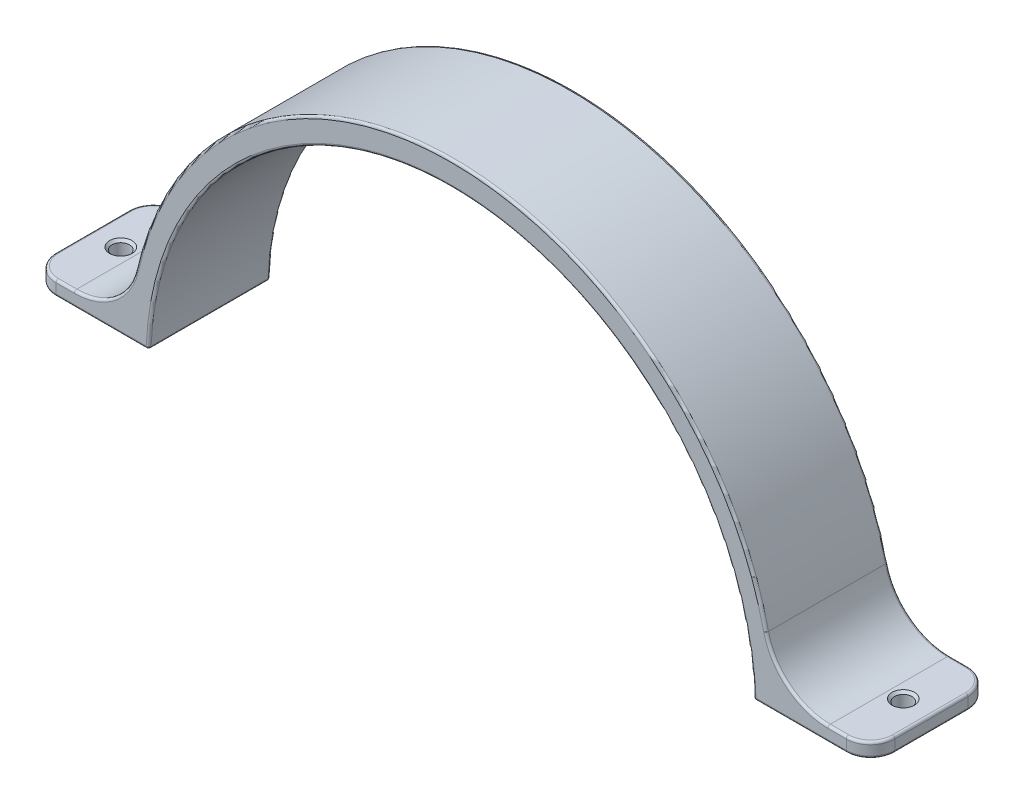
SolidWorks part; units mm, degrees
ref_plane "Plano frontal" through (0, 0, 0) normal (0, 0, 1) x (1, 0, 0)
ref_plane "Plano superior" through (0, 0, 0) normal (0, 1, 0) x (1, 0, 0)
ref_plane "Plano direito" through (0, 0, 0) normal (1, 0, 0) x (0, 0, -1)
sketch "Sketch1" plane through (0, 0, 0) normal (0, 0, 1) x (1, 0, 0)
  line L0 (0, -13.75) -> (0, 13.75) construction
  line L1 (-86.15, -27) -> (-66.15, -27)
  line L2 (-86.15, -27) -> (-86.15, -30)
  line L3 (-86.15, -30) -> (-62.15, -30)
  line L4 (86.15, -30) -> (62.15, -30)
  line L5 (86.15, -27) -> (86.15, -30)
  line L6 (86.15, -27) -> (66.15, -27)
  line L7 (-62.15, -30) -> (62.15, -30) construction
  line L8 (0, 30) -> (0, -30) construction
  arc A2 (-62.15, -30) -> (62.15, -30) centre (0, -32.1885) cw
  arc A3 (-66.15, -27) -> (66.15, -27) centre (0, -31.2889) cw
  point P4 (20.0951, 6.1437)
  point P15 (16.9603, 5.1853)
  point P16 (0, 0)
  dimension "D3" = 4
  dimension "D4" = 124.3
  dimension "D5" = 5
  dimension "D6" = 60
  dimension "D1" = 3
  dimension "D2" = 20
extrude "Boss-Extrude1" add sketch "Sketch1" along normal mid plane 25
sketch "Sketch2" plane through (0, 0, 0) normal (0, 1, 0) x (1, 0, 0)
  line L3 (0, -13.75) -> (0, 13.75) construction
  line L5 (-86.15, -12.5) -> (-86.15, 12.5) construction
  line L7 (-66.15, -12.5) -> (-66.15, 12.5) construction
  line L8 (-66.15, 12.5) -> (-86.15, 12.5) construction
  line L9 (-66.15, -12.5) -> (-86.15, -12.5) construction
  circle A0 centre (-80.35, 0) radius 1.5 construction
  circle A1 centre (-80.35, 0) radius 1.8
  circle A2 centre (80.35, 0) radius 1.5 construction
  circle A3 centre (80.35, 0) radius 1.8
  dimension "D1" = 3
  dimension "D3" = 4
  dimension "D4" = 12.4
  dimension "D5" = 12.5
  dimension "D6" = 12.5
  dimension "D7" = 160.7
  dimension "D2" = 0.3
extrude "Cut-Extrude4" cut sketch "Sketch2" against normal through all both and the other way through all
chamfer "Chamfer1" distance 0.5 angle 45 2 edges at (-80.35, -27, -1.8) (80.35, -27, -1.8)
fillet "Fillet1" radius 13 2 edges at (-66.15, -27, 0) (66.15, -27, 0)
fillet "Fillet2" radius 5 4 edges at (86.15, -28.5, 12.5) (86.15, -28.5, -12.5) (-86.15, -28.5, -12.5) (-86.15, -28.5, 12.5)
fillet "Fillet3" radius 0.5 30 edges at (-84.6855, -30, -11.0355) (-86.15, -30, 0) (-84.6855, -30, 11.0355) (84.6855, -27, 11.0355) (86.15, -27, 0) (84.6855, -27, -11.0355) (-84.6855, -27, -11.0355) (-86.15, -27, 0) (-84.6855, -27, 11.0355) (84.6855, -30, -11.0355) (86.15, -30, 0) (84.6855, -30, 11.0355) (-62.15, -30, 0) (62.15, -30, 0) (69.2524, -24.1452, -12.5) (0, 35, -12.5) (-69.2524, -24.1452, -12.5) (-79.2655, -27, -12.5) (-71.65, -30, -12.5) (0, 30, -12.5) (71.65, -30, -12.5) (79.2655, -27, -12.5) (0, 30, 12.5) (-71.65, -30, 12.5) (-79.2655, -27, 12.5) (-69.2524, -24.1452, 12.5) (0, 35, 12.5) (69.2524, -24.1452, 12.5) (79.2655, -27, 12.5) (71.65, -30, 12.5)
